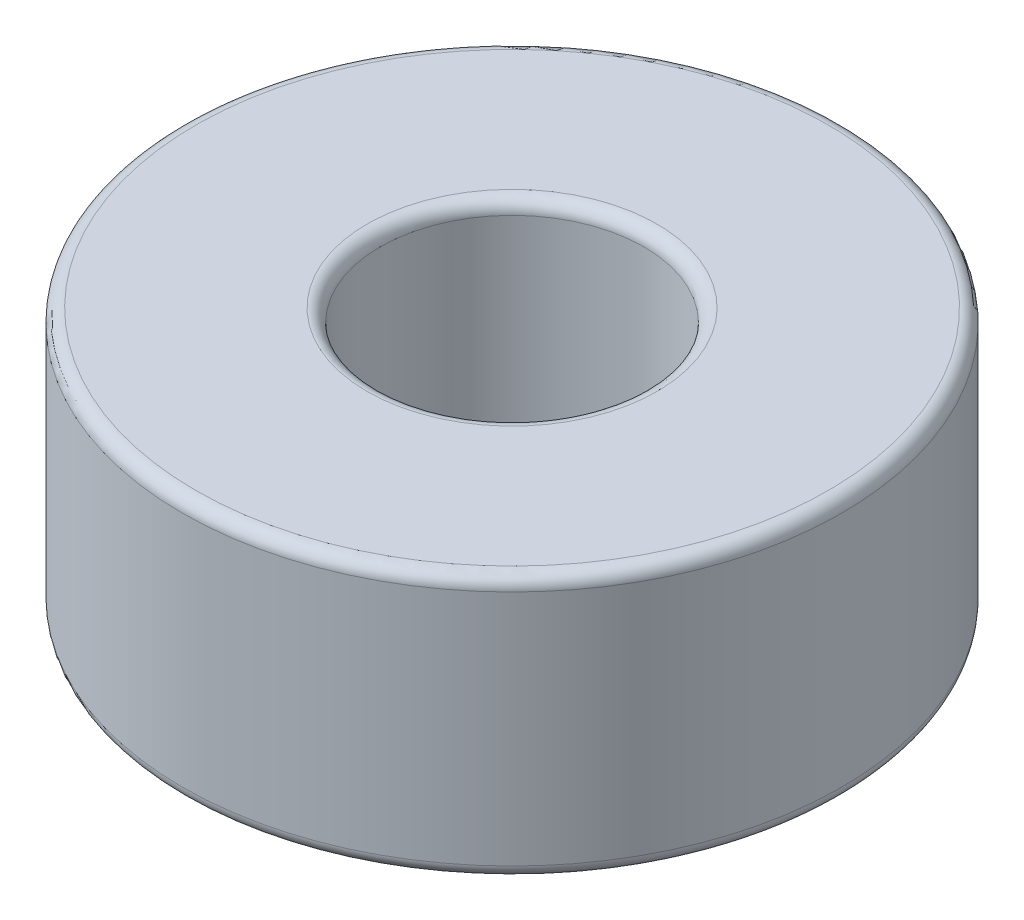
SolidWorks part; units mm, degrees
material "acero"
ref_plane "Alzado" through (0, 0, 0) normal (0, 0, 1) x (1, 0, 0)
ref_plane "Planta" through (0, 0, 0) normal (0, 1, 0) x (1, 0, 0)
ref_plane "Vista lateral" through (0, 0, 0) normal (1, 0, 0) x (0, 0, -1)
sketch "Sketch1" plane through (0, 0, 0) normal (0, 1, 0) x (1, 0, 0)
  circle A0 centre (0, 0) radius 7.5
  circle A1 centre (0, 0) radius 3
  dimension "D1" = 15
  dimension "D2" = 6
extrude "Boss-Extrude1" add sketch "Sketch1" along normal mid plane 6
fillet "Fillet1" radius 0.3 4 edges at (0, -3, 7.5) (0, 3, 7.5) (0, -3, 3) (0, 3, 3)
